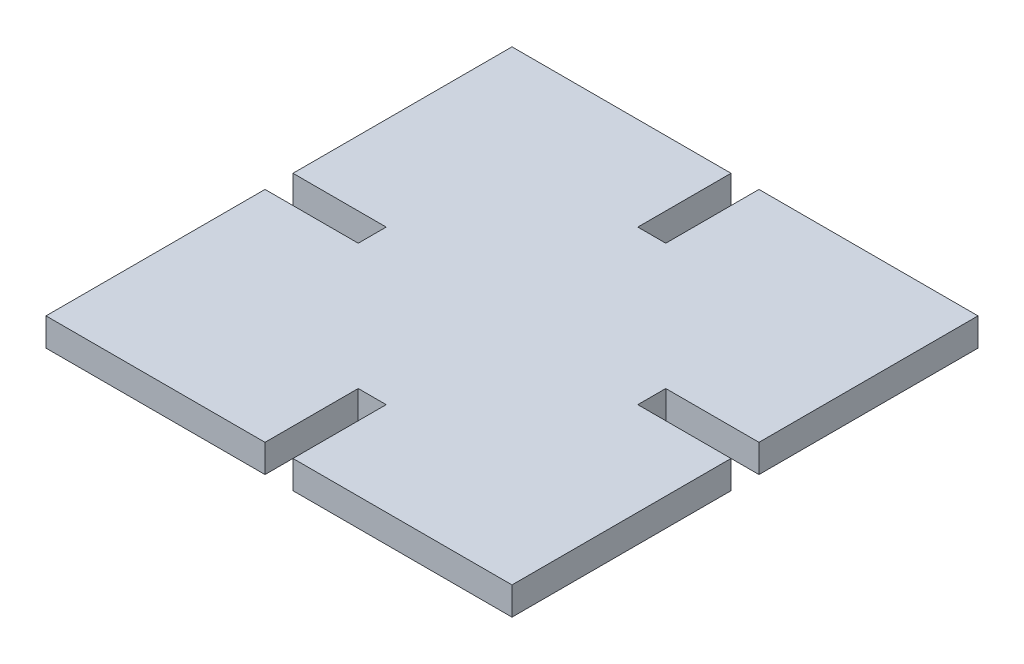
SolidWorks part; units mm, degrees
ref_plane "Front" through (0, 0, 0) normal (0, 0, 1) x (1, 0, 0)
ref_plane "Top" through (0, 0, 0) normal (0, 1, 0) x (1, 0, 0)
ref_plane "Right" through (0, 0, 0) normal (1, 0, 0) x (0, 0, -1)
sketch "Sketch1" plane through (0, 0, 0) normal (0, 1, 0) x (1, 0, 0)
  line L0 (-1.5, 25) -> (-1.5, 15)
  line L1 (-25, 25) -> (-1.5, 25)
  line L2 (-25, 25) -> (-25, 1.5)
  line L3 (-25, -25) -> (-1.5, -25)
  line L4 (25, 25) -> (25, 1.5)
  line L5 (-25, 25) -> (25, -25) construction
  line L6 (-25, -25) -> (25, 25) construction
  line L7 (-1.5, 15) -> (1.5, 15)
  line L8 (1.5, 15) -> (1.5, 25)
  line L9 (-25, 1.5) -> (-15, 1.5)
  line L10 (-15, 1.5) -> (-15, -1.5)
  line L11 (-15, -1.5) -> (-25, -1.5)
  line L12 (-1.5, -25) -> (-1.5, -15)
  line L13 (-1.5, -15) -> (1.5, -15)
  line L14 (1.5, -15) -> (1.5, -25)
  line L15 (25, 1.5) -> (15, 1.5)
  line L16 (15, 1.5) -> (15, -1.5)
  line L17 (15, -1.5) -> (25, -1.5)
  line L18 (1.5, 25) -> (25, 25)
  line L19 (-25, -1.5) -> (-25, -25)
  line L20 (1.5, -25) -> (25, -25)
  line L21 (25, -1.5) -> (25, -25)
  point P0 (0, 0)
  point P21 (-6.4121, 25)
  point P23 (3.9625, 25)
  point P24 (0, 15)
  point P25 (0, -15)
  point P26 (-13.4726, -4.2507)
  point P27 (11.5994, -4.2507)
  point P28 (-15, 0)
  point P29 (15, 0)
  point P30 (0, 0)
  dimension "D1" = 50
  dimension "D2" = 50
  dimension "D3" = 3
  dimension "D4" = 10
extrude "Boss-Extrude1" add sketch "Sketch1" along normal blind 3 contours L8 L18 L4 L15 L16 L17 L21 L20 L14 L13 L12 L3 L19 L11 L10 L9 L2 L1 L0 L7
